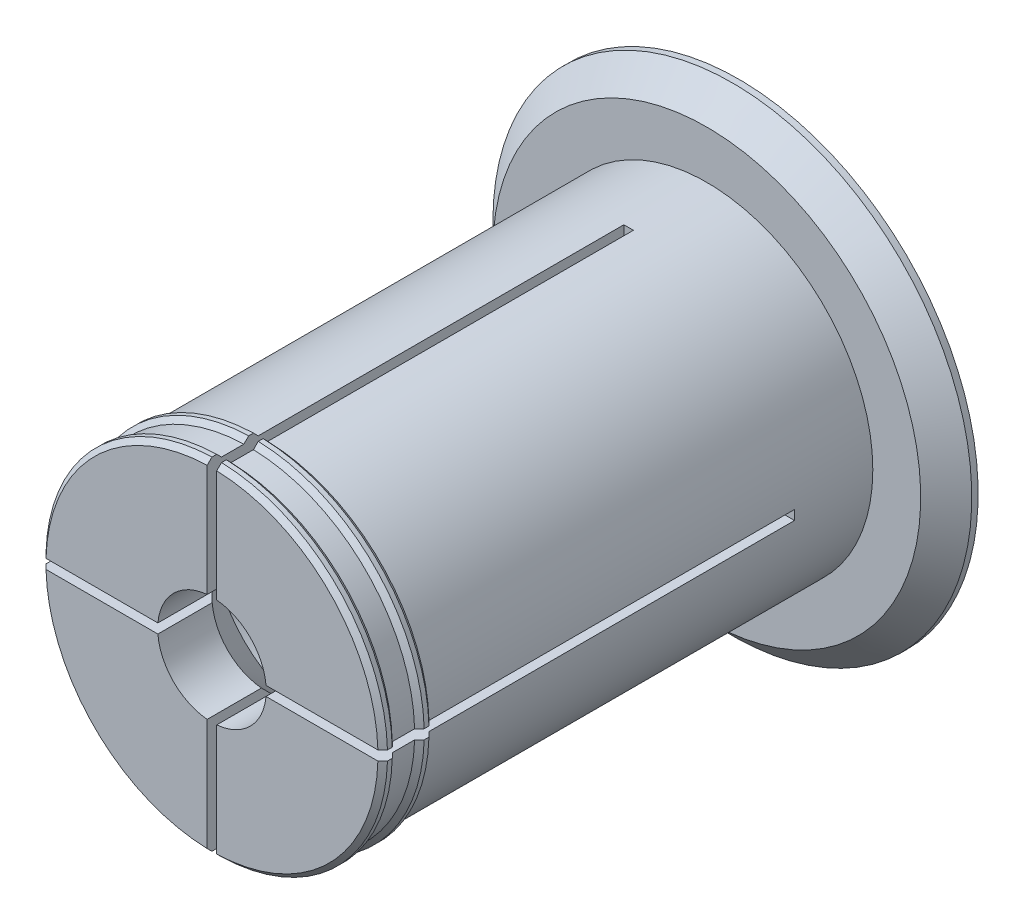
SolidWorks part; units mm, degrees
ref_plane "Front" through (0, 0, 0) normal (0, 0, 1) x (1, 0, 0)
ref_plane "Top" through (0, 0, 0) normal (0, 1, 0) x (1, 0, 0)
ref_plane "Right" through (0, 0, 0) normal (1, 0, 0) x (0, 0, -1)
sketch "Axle base sketch" plane through (0, 0, 0) normal (0, 0, 1) x (1, 0, 0)
  circle A0 centre (0, 0) radius 26
  dimension "D1" = 52
extrude "Axle" add sketch "Axle base sketch" along normal blind 77.5
sketch "Guard base" plane through (0, 0, 0) normal (0, 0, -1) x (-1, 0, 0)
  circle A0 centre (0, 0) radius 37.5
  dimension "D1" = 75
extrude "Guard" add sketch "Guard base" along normal blind 5
sketch "Inner axle hole base" plane through (0, 0, 77.5) normal (0, 0, 1) x (1, 0, 0)
  circle A0 centre (0, 0) radius 8.5
  dimension "D1" = 17
extrude "Inner axle hole" cut sketch "Inner axle hole base" against normal through all
sketch "Mate ring base" plane through (0, 0, 0) normal (0, 1, 0) x (1, 0, 0)
  line L0 (26, -77.5) -> (26.75, -76.75)
  line L1 (26.75, -76.75) -> (26.75, -76)
  line L2 (26.75, -76) -> (26, -75.25)
  line L3 (26.75, -76.75) -> (26.75, -77.5) construction
  line L4 (26.75, -77.5) -> (26, -77.5) construction
  line L5 (26, -75.25) -> (26, -77.5)
  line L6 (26, -77.5) -> (26, 0) construction
  line L8 (26, -71.75) -> (26.75, -71)
  line L9 (26.75, -71) -> (26.75, -70.25)
  line L10 (26.75, -70.25) -> (26, -69.5)
  line L11 (26, -69.5) -> (26, -71.75)
  dimension "D1" = 0.75
  dimension "D2" = 0.75
  dimension "D3" = 5
  dimension "D4" = 0.75
ref_axis "Center Z" through (0, 0, 0) along (0, 0, -1)
revolve "Mate rings" add sketch "Mate ring base" angle 360 about axis through (0, 0, 0) along (0, 0, -1)
sketch "Inner mass remove base" plane through (0, 0, 0) normal (1, 0, 0) x (0, 0, -1)
  line L0 (-77.5, 0) -> (-60.25, -17.25)
  line L1 (-60.25, -17.25) -> (-12.25, -17.25)
  line L2 (-12.25, -17.25) -> (5, 0)
  line L3 (5, 0) -> (-77.5, 0)
  line L4 (5, -8.5) -> (5, 8.5) construction
  line L5 (-60.25, -17.25) -> (-60.25, -8.5) construction
  line L6 (-60.25, -17.25) -> (-60.25, -26) construction
  line L7 (-77.5, 8.5) -> (-77.5, -8.5) construction
  point P9 (-77.5, -8.5)
  point P11 (-77.5, -26)
  dimension "D1" = 135
revolve "Inner mass remove" cut sketch "Inner mass remove base" angle 360 about axis through (0, 0, 0) along (0, 0, -1)
ref_point "Bend room endpoint"
sketch "Bend room base" plane through (0, 0, 77.5) normal (0, 0, 1) x (1, 0, 0)
  line L0 (0.75, -37.5) -> (0.75, 37.5)
  line L1 (0.75, 37.5) -> (-0.75, 37.5)
  line L2 (-0.75, 37.5) -> (-0.75, -37.5)
  line L3 (-0.75, -37.5) -> (0.75, -37.5)
  dimension "D1" = 0.75
  dimension "D2" = 0.75
  dimension "D3" = 37.5
  dimension "D4" = 37.5
extrude "Bend room 1" cut sketch "Bend room base" against normal up to vertex (28.9925 mm away)
pattern_circular "Bend room 2" count 2 every 90 about axis through (0, 0, 0) along (0, 0, -1) of "Bend room 1"
chamfer "Easy removal chamfer" distance 4 angle 45 1 edges at (-37.5, 0, 0)
equation "\"32_92_spool_inner_diameter\"=32"
equation "\"D1@Axle base sketch\"  = \"53_71_spool_inner_diameter\" - \"spool_inner_diameter_room\""
equation "\"spool_inner_diameter_room\"=1"
equation "\"32_92_spool_thickness\"=92"
equation "\"D1@Axle\"  = \"53_71_spool_thickness\" + \"guard_thickness\" + \"removal_room\" * 2"
equation "\"32_92_guard_diameter\"=50"
equation "\"D1@Guard base\"  = \"53_71_guard_diameter\""
equation "\"guard_thickness\"=5"
equation "\"D1@Guard\"=\"guard_thickness\""
equation "\"large_inner_axle_diameter\"=20"
equation "\"D1@Inner axle hole base\"=\"small_inner_axle_diameter\""
equation "\"mate_room\"= 0.25"
equation "\"removal_room\"= 0.75"
equation "\"small_inner_axle_diameter\"=17"
equation "\"53_55_spool_inner_diameter\"=53"
equation "\"53_55_spool_thickness\"=55"
equation "\"53_55_guard_diameter\"=75"
equation "\"D1@Mate ring base\"=\"removal_room\""
equation "\"D2@Mate ring base\"=\"removal_room\""
equation "\"D3@Mate ring base\"=\"guard_thickness\""
equation "\"D4@Mate ring base\"=\"removal_room\""
equation "\"D1@Bend room base\" = \"removal_room\""
equation "\"D2@Bend room base\"=\"removal_room\""
equation "\"D3@Bend room base\" = \"53_71_guard_diameter\" / 2"
equation "\"D4@Bend room base\"  = \"53_71_guard_diameter\" / 2"
equation "\"bend_room_length_multiplier\"=3"
equation "\"D1@Easy removal chamfer\"=\"guard_thickness\"-1"
equation "\"32_92_extra_spool_thickness\"=-5"
equation "\"39_92_spool_inner_diameter\"=39"
equation "\"39_92_spool_thickness\"=92"
equation "\"39_92_guard_diameter\"=60"
equation "\"52_62_spool_inner_diameter\"=52"
equation "\"52_62_spool_thickness\"=62"
equation "\"52_62_guard_diameter\"=75"
equation "\"53_71_spool_inner_diameter\"=53"
equation "\"53_71_spool_thickness\"=71"
equation "\"53_71_guard_diameter\"=75"
